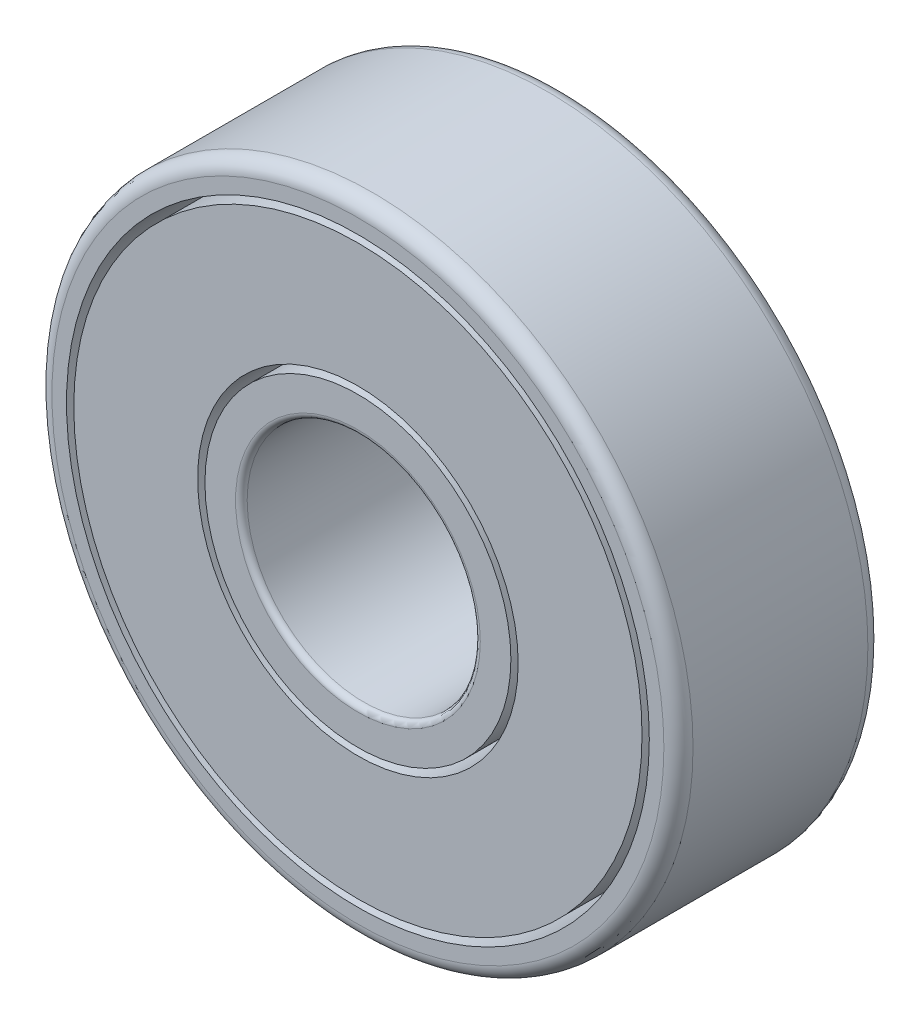
SolidWorks part; units mm, degrees
material "AISI 304"
ref_plane "Alzado" through (0, 0, 0) normal (0, 0, 1) x (1, 0, 0)
ref_plane "Planta" through (0, 0, 0) normal (0, 1, 0) x (1, 0, 0)
ref_plane "Vista lateral" through (0, 0, 0) normal (1, 0, 0) x (0, 0, -1)
sketch "Croquis1" plane through (0, 0, 0) normal (0, 0, 1) x (1, 0, 0)
  circle A0 centre (0, 0) radius 4
  circle A1 centre (0, 0) radius 5.25
  circle A2 centre (0, 0) radius 5.5
  circle A3 centre (0, 0) radius 9.75
  circle A4 centre (0, 0) radius 10
  circle A5 centre (0, 0) radius 11
  dimension "D1" = 22
  dimension "D2" = 8
  dimension "D3" = 11
  dimension "D4" = 20
  dimension "D5" = 10.5
  dimension "D6" = 19.5
extrude "Saliente-Extruir1" add sketch "Croquis1" along normal blind 7 contours A3 A2 | A1 A0 | A5 A4
fillet "Redondeo1" radius 0.2 2 edges at (4, 0, 0) (4, 0, 7)
fillet "Redondeo2" radius 0.5 2 edges at (11, 0, 0) (11, 0, 7)
